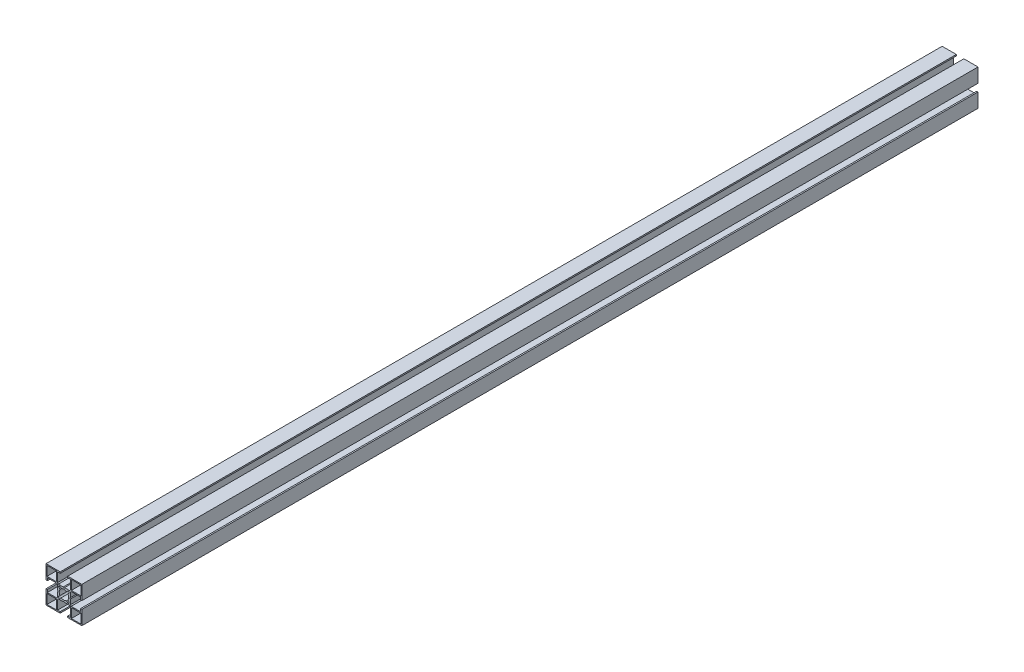
SolidWorks part; units mm, degrees
material "6063 T5"
ref_plane "Спереди" through (0, 0, 0) normal (0, 0, 1) x (1, 0, 0)
ref_plane "Сверху" through (0, 0, 0) normal (0, 1, 0) x (1, 0, 0)
ref_plane "Справа" through (0, 0, 0) normal (1, 0, 0) x (0, 0, -1)
sketch "Эскиз1" plane through (0, 0, 0) normal (0, 0, 1) x (1, 0, 0)
  line L0 (-12.3299, 71.8306) -> (27.6701, 71.8306) construction
  line L1 (0, 20) -> (0, -20) construction
  line L2 (-20, 0) -> (20, 0) construction
  line L3 (-20, 7.15) -> (-20, 20)
  line L4 (-20, 20) -> (-7.15, 20)
  line L5 (7.15, 20) -> (20, 20)
  line L6 (20, 20) -> (20, 7.15)
  line L7 (20, -7.15) -> (20, -20)
  line L8 (20, -20) -> (7.15, -20)
  line L9 (-7.15, -20) -> (-20, -20)
  line L10 (-20, -20) -> (-20, -7.15)
  line L11 (18.9, 8.3) -> (8.3, 8.3)
  line L12 (-18.9, 18.9) -> (-8.3, 18.9)
  line L13 (-18.9, 18.9) -> (-18.9, 8.3)
  line L14 (-18.9, 8.3) -> (-8.3, 8.3)
  line L15 (-8.3, 18.9) -> (-8.3, 8.3)
  line L16 (8.3, 18.9) -> (8.3, 8.3)
  line L17 (18.9, 18.9) -> (8.3, 18.9)
  line L18 (18.9, 18.9) -> (18.9, 8.3)
  line L19 (8.3, -18.9) -> (8.3, -8.3)
  line L20 (18.9, -8.3) -> (8.3, -8.3)
  line L21 (18.9, -18.9) -> (18.9, -8.3)
  line L22 (18.9, -18.9) -> (8.3, -18.9)
  line L23 (-18.9, -8.3) -> (-8.3, -8.3)
  line L24 (-8.3, -18.9) -> (-8.3, -8.3)
  line L25 (-18.9, -18.9) -> (-8.3, -18.9)
  line L26 (-18.9, -18.9) -> (-18.9, -8.3)
  point P10 (0, 0)
  point P39 (0, 0)
  line B0 (-20, 7.15) -> (-20, 4.2)
  line B1 (-20, 4.2) -> (-18.5, 4.2)
  line B2 (-18.5, 4.2) -> (-18.5, 7.15)
  line B3 (-18.5, 7.15) -> (-8.15, 7.15)
  line B4 (-8.15, 7.15) -> (-7.15, 6.15)
  line B5 (-7.15, 6.15) -> (-7.15, 0.7)
  line B6 (-7.15, 0.7) -> (-6.45, 0)
  line B7 (-6.45, 0) -> (-20, 0) construction
  line B8 (-7.15, -0.7) -> (-6.45, 0)
  line B9 (-7.15, -6.15) -> (-7.15, -0.7)
  line B10 (-8.15, -7.15) -> (-7.15, -6.15)
  line B11 (-18.5, -7.15) -> (-8.15, -7.15)
  line B12 (-18.5, -4.2) -> (-18.5, -7.15)
  line B13 (-20, -4.2) -> (-18.5, -4.2)
  line B14 (-20, -7.15) -> (-20, -4.2)
  line B15 (0, 0) -> (4.9497, 4.9497) construction
  line B16 (0, 0) -> (0, 3.4) construction
  line B17 (0, 0) -> (3.4, 0) construction
  line B18 (4.2426, 5.6569) -> (2.9372, 4.3515)
  line B19 (5.6569, 4.2426) -> (4.3515, 2.9372)
  line B20 (-4.2426, 5.6569) -> (-2.9372, 4.3515)
  line B21 (-5.6569, 4.2426) -> (-4.3515, 2.9372)
  line B22 (-5.6569, -4.2426) -> (-4.3515, -2.9372)
  line B23 (-4.2426, -5.6569) -> (-2.9372, -4.3515)
  line B24 (4.2426, -5.6569) -> (2.9372, -4.3515)
  line B25 (5.6569, -4.2426) -> (4.3515, -2.9372)
  arc B26 (4.3515, -2.9372) -> (4.3515, 2.9372) centre (0, 0) ccw
  arc B27 (4.2426, 5.6569) -> (5.6569, 4.2426) centre (4.9497, 4.9497) cw
  arc B28 (2.9372, 4.3515) -> (-2.9372, 4.3515) centre (0, 0) ccw
  arc B29 (-4.2426, 5.6569) -> (-5.6569, 4.2426) centre (-4.9497, 4.9497) ccw
  arc B30 (-4.3515, -2.9372) -> (-4.3515, 2.9372) centre (0, 0) cw
  arc B31 (-4.2426, -5.6569) -> (-5.6569, -4.2426) centre (-4.9497, -4.9497) cw
  arc B32 (2.9372, -4.3515) -> (-2.9372, -4.3515) centre (0, 0) cw
  arc B33 (4.2426, -5.6569) -> (5.6569, -4.2426) centre (4.9497, -4.9497) ccw
  line B34 (7.15, 20) -> (4.2, 20)
  line B35 (4.2, 20) -> (4.2, 18.5)
  line B36 (4.2, 18.5) -> (7.15, 18.5)
  line B37 (7.15, 18.5) -> (7.15, 8.15)
  line B38 (7.15, 8.15) -> (6.15, 7.15)
  line B39 (6.15, 7.15) -> (0.7, 7.15)
  line B40 (0.7, 7.15) -> (0, 6.45)
  line B41 (0, 6.45) -> (0, 20) construction
  line B42 (-0.7, 7.15) -> (0, 6.45)
  line B43 (-6.15, 7.15) -> (-0.7, 7.15)
  line B44 (-7.15, 8.15) -> (-6.15, 7.15)
  line B45 (-7.15, 18.5) -> (-7.15, 8.15)
  line B46 (-4.2, 18.5) -> (-7.15, 18.5)
  line B47 (-4.2, 20) -> (-4.2, 18.5)
  line B48 (-7.15, 20) -> (-4.2, 20)
  line B49 (20, -7.15) -> (20, -4.2)
  line B50 (20, -4.2) -> (18.5, -4.2)
  line B51 (18.5, -4.2) -> (18.5, -7.15)
  line B52 (18.5, -7.15) -> (8.15, -7.15)
  line B53 (8.15, -7.15) -> (7.15, -6.15)
  line B54 (7.15, -6.15) -> (7.15, -0.7)
  line B55 (7.15, -0.7) -> (6.45, 0)
  line B56 (6.45, 0) -> (20, 0) construction
  line B57 (7.15, 0.7) -> (6.45, 0)
  line B58 (7.15, 6.15) -> (7.15, 0.7)
  line B59 (8.15, 7.15) -> (7.15, 6.15)
  line B60 (18.5, 7.15) -> (8.15, 7.15)
  line B61 (18.5, 4.2) -> (18.5, 7.15)
  line B62 (20, 4.2) -> (18.5, 4.2)
  line B63 (20, 7.15) -> (20, 4.2)
  line B64 (-7.15, -20) -> (-4.2, -20)
  line B65 (-4.2, -20) -> (-4.2, -18.5)
  line B66 (-4.2, -18.5) -> (-7.15, -18.5)
  line B67 (-7.15, -18.5) -> (-7.15, -8.15)
  line B68 (-7.15, -8.15) -> (-6.15, -7.15)
  line B69 (-6.15, -7.15) -> (-0.7, -7.15)
  line B70 (-0.7, -7.15) -> (0, -6.45)
  line B71 (0, -6.45) -> (0, -20) construction
  line B72 (0.7, -7.15) -> (0, -6.45)
  line B73 (6.15, -7.15) -> (0.7, -7.15)
  line B74 (7.15, -8.15) -> (6.15, -7.15)
  line B75 (7.15, -18.5) -> (7.15, -8.15)
  line B76 (4.2, -18.5) -> (7.15, -18.5)
  line B77 (4.2, -20) -> (4.2, -18.5)
  line B78 (7.15, -20) -> (4.2, -20)
  dimension "D1" = 40
  dimension "D2" = 40
  dimension "D3" = 4
  dimension "D4" = 10.6
  dimension "D5" = 10.6
  dimension "D6" = 1.1
  dimension "D7" = 1.1
  dimension "D8" = 4
sketch_block_instance "Блок1-1"
sketch_block "Блок1" parameters "D1"=14.3, "D2"=8.4, "D3"=12.85, "D4"=1, "D5"=135, "D6"=0.7, "D7"=1.5
sketch_block_instance "O6,8Х-1"
sketch_block "O6,8Х" parameters "D2"=10.5, "D1"=45, "D3"=2, "D4"=7
sketch_block_instance "Блок1-5"
sketch_block_instance "Блок1-6"
sketch_block_instance "Блок1-7"
extrude "Бобышка-Вытянуть1" add sketch "Эскиз1" along normal blind 1000 contours B78 L8 L7 B49 B50 B51 B52 B53 B54 B55 B57 B58 B59 B60 B61 B62 B63 L6 L5 B34 B35 B36 B37 B38 B39 B40 B42 B43 B44 B45 B46 B47 B48 L4 L3 B0 B1 B2 B3 B4 B5 B6 B8 B9 B10 B11 B12 B13 B14 L10 L9
